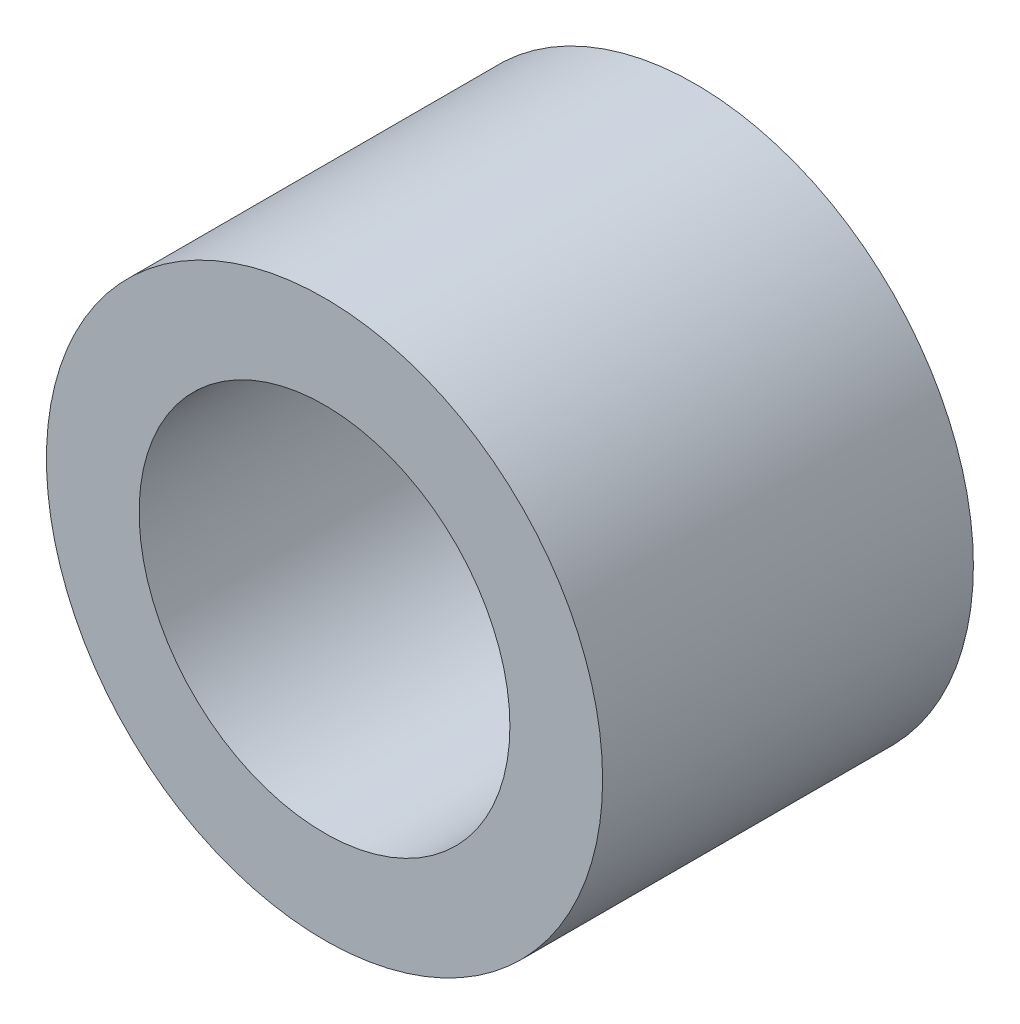
SolidWorks part; units mm, degrees
ref_plane "Front Plane" through (0, 0, 0) normal (0, 0, 1) x (1, 0, 0)
ref_plane "Top Plane" through (0, 0, 0) normal (0, 1, 0) x (1, 0, 0)
ref_plane "Right Plane" through (0, 0, 0) normal (1, 0, 0) x (0, 0, -1)
sketch "Sketch1" plane through (0, 0, 0) normal (0, 0, 1) x (1, 0, 0)
  circle A0 centre (0, 0) radius 6
  circle A1 centre (0, 0) radius 4
  dimension "D1" = 12
  dimension "ID" = 8
extrude "Extrude1" add sketch "Sketch1" along normal mid plane 8
sketch "Sketch2" plane through (0, 0, 0) normal (1, 0, 0) x (0, 0, -1)
  line L0 (-4, -4) -> (4, -4) construction
  line L3 (4, 4) -> (-4, 4) construction
  line L5 (-4, -4) -> (4, -4)
  line L6 (4, 4) -> (-4, 4)
sketch "Sketch4" plane through (0, 0, 4) normal (0, 0, 1) x (1, 0, 0)
  line L0 (0, 0) -> (-2.8284, 2.8284)
  line L1 (0, -19.25) -> (0, 19.25) construction
  circle A0 centre (0, 0) radius 4 construction
  dimension "D1" = 45
